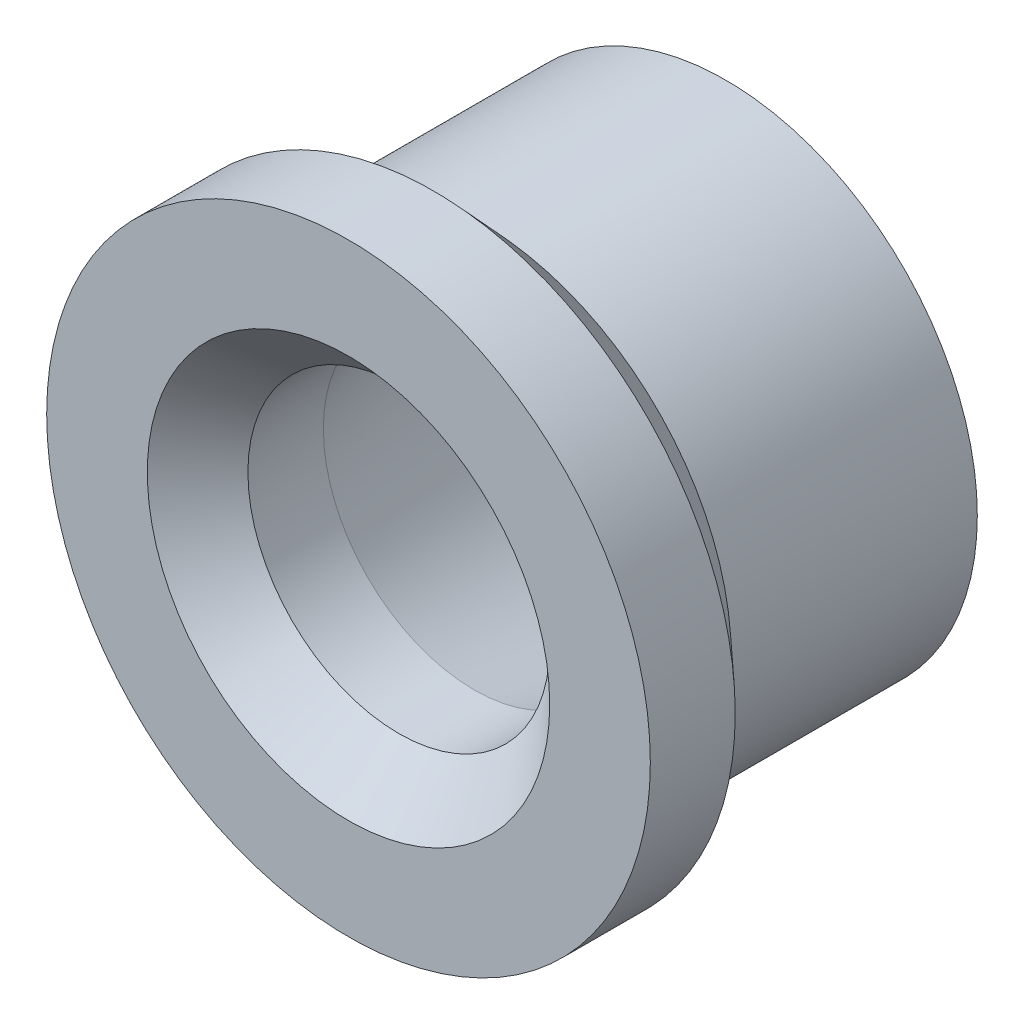
SolidWorks part; units mm, degrees
ref_plane "Alzado" through (0, 0, 0) normal (0, 0, 1) x (1, 0, 0)
ref_plane "Planta" through (0, 0, 0) normal (0, 1, 0) x (1, 0, 0)
ref_plane "Vista lateral" through (0, 0, 0) normal (1, 0, 0) x (0, 0, -1)
sketch "Croquis1" plane through (0, 0, 0) normal (0, 1, 0) x (1, 0, 0)
  line L0 (0, 3.75) -> (0, -3.75) construction
  line L1 (0, 3.75) -> (-5, 3.75)
  line L2 (-5, 3.75) -> (-5, -1.1405)
  line L3 (-5, -1.1405) -> (-6, -2.0622)
  line L4 (-6, -2.0622) -> (-6, -3.75)
  line L5 (-6, -3.75) -> (0, -3.75)
  line L6 (0, 3.75) -> (0, -3.75)
  line L7 (0, -1.25) -> (-3, -1.25)
  line L8 (-3, -1.25) -> (-4, 3.75)
  point P8 (0, 0)
  dimension "D1" = 5
  dimension "D2" = 4.8905
  dimension "D3" = 7.5
  dimension "D4" = 6
  dimension "D5" = 1.36
  dimension "D6" = 3
  dimension "D7" = 1
  dimension "D8" = 5
revolve "Revolución1" add sketch "Croquis1" angle 360 about L0
sketch "Croquis2" plane through (0, 0, 3.75) normal (0, 0, 1) x (1, 0, 0)
  circle A0 centre (0, 0) radius 3
  dimension "D1" = 6
extrude "Cortar-Extruir1" cut sketch "Croquis2" against normal blind 10 contours A0
chamfer "Chaflán1" distance 1 angle 45 1 edges at (3, 0, 3.75)
